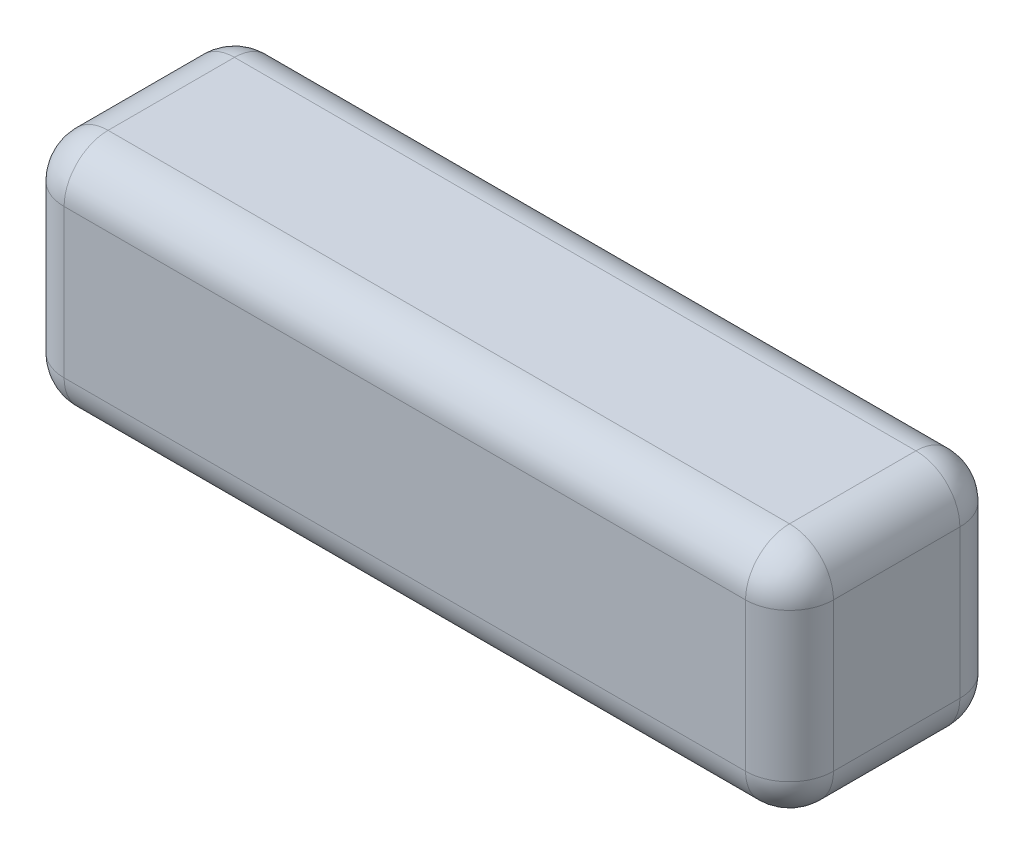
SolidWorks part; units mm, degrees
ref_plane "Front Plane" through (0, 0, 0) normal (0, 0, 1) x (1, 0, 0)
ref_plane "Top Plane" through (0, 0, 0) normal (0, 1, 0) x (1, 0, 0)
ref_plane "Right Plane" through (0, 0, 0) normal (1, 0, 0) x (0, 0, -1)
sketch "Sketch1" plane through (0, 0, 0) normal (0, 1, 0) x (1, 0, 0)
  line L1 (0, 0) -> (140, 0)
  line L2 (0, 0) -> (0, -39)
  line L3 (0, -39) -> (140, -39)
  line L4 (140, 0) -> (140, -39)
  dimension "D1" = 39
  dimension "D2" = 140
extrude "Boss-Extrude1" add sketch "Sketch1" along normal blind 43
fillet "Fillet1" radius 8 12 edges at (0, 21.5, 39) (140, 21.5, 39) (140, 21.5, 0) (0, 21.5, 0) (70, 43, 0) (140, 43, 19.5) (70, 43, 39) (0, 43, 19.5) (70, 0, 0) (140, 0, 19.5) (70, 0, 39) (0, 0, 19.5)
